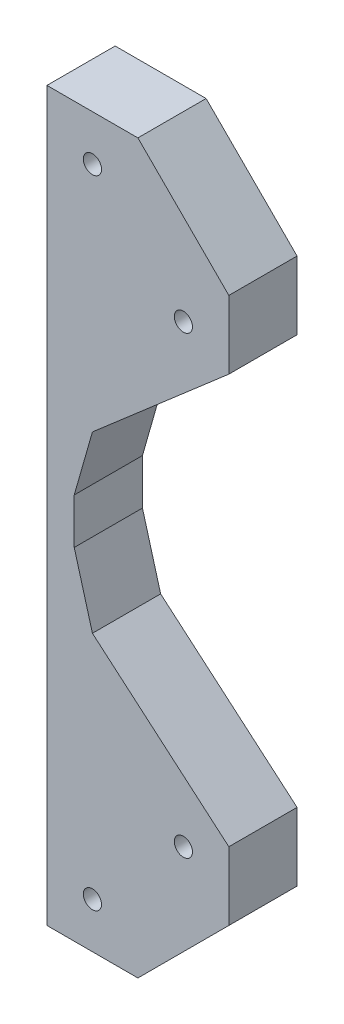
SolidWorks part; units mm, degrees
material "Náilon 101"
ref_plane "Plano frontal" through (0, 0, 0) normal (0, 0, 1) x (1, 0, 0)
ref_plane "Plano superior" through (0, 0, 0) normal (0, 1, 0) x (1, 0, 0)
ref_plane "Plano direito" through (0, 0, 0) normal (1, 0, 0) x (0, 0, -1)
sketch "Esboço1" plane through (0, 0, 0) normal (0, 0, 1) x (1, 0, 0)
  line L0 (0, 85.0753) -> (20, 85.0753)
  line L1 (20, 85.0753) -> (40, 65.0753)
  line L2 (40, 65.0753) -> (40, 50.0753)
  line L3 (40, 50.0753) -> (10, 24.0753)
  line L4 (6, 10.075) -> (10, 24.0753)
  line L5 (6, 10.075) -> (6, 0.075)
  line L6 (6, 0.075) -> (10, -14.2721)
  line L7 (10, -14.2721) -> (40, -39.9253)
  line L8 (40, -39.9253) -> (40, -54.9247)
  line L9 (20, -74.9247) -> (40, -54.9247)
  line L10 (20, -74.9247) -> (0, -74.9247)
  line L11 (0, -74.9247) -> (0, 85.0753)
  circle A0 centre (10, 75.0753) radius 2
  circle A1 centre (30, 55.0753) radius 2
  circle A2 centre (30, -44.9247) radius 2
  circle A3 centre (10, -64.9247) radius 2
extrude "Ressalto-extrusão1" add sketch "Esboço1" along normal blind 15
sketch "Esboço2" plane through (0, 0, 15) normal (0, 0, 1) x (1, 0, 0)
  line L12 (0, 85.0753) -> (0, -74.9247)
  line L13 (0, -74.9247) -> (20, -74.9247)
  line L14 (20, -74.9247) -> (40, -54.9247)
  line L15 (40, -54.9247) -> (40, -39.9253)
  line L16 (40, -39.9253) -> (10, -14.2721)
  line L17 (10, -14.2721) -> (6, 0.075)
  line L18 (6, 0.075) -> (6, 10.075)
  line L19 (6, 10.075) -> (10, 24.0753)
  line L20 (10, 24.0753) -> (40, 50.0753)
  line L21 (40, 50.0753) -> (40, 65.0753)
  line L22 (40, 65.0753) -> (20, 85.0753)
  line L23 (20, 85.0753) -> (0, 85.0753)
  line L24 (0, 85.0753) -> (0, -74.9247)
  line L25 (0, -74.9247) -> (20, -74.9247)
  line L26 (20, -74.9247) -> (40, -54.9247)
  line L27 (40, -54.9247) -> (40, -39.9253)
  line L28 (40, -39.9253) -> (10, -14.2721)
  line L29 (10, -14.2721) -> (6, 0.075)
  line L30 (6, 0.075) -> (6, 10.075)
  line L31 (6, 10.075) -> (10, 24.0753)
  line L32 (10, 24.0753) -> (40, 50.0753)
  line L33 (40, 50.0753) -> (40, 65.0753)
  line L34 (40, 65.0753) -> (20, 85.0753)
  line L35 (20, 85.0753) -> (0, 85.0753)
  circle A0 centre (30, -44.9247) radius 2 construction
  circle A1 centre (10, -64.9247) radius 2 construction
  circle A2 centre (30, 55.0753) radius 2 construction
  circle A3 centre (10, 75.0753) radius 2 construction
  circle A4 centre (30, -44.9247) radius 2
  circle A5 centre (10, -64.9247) radius 2
  circle A6 centre (30, 55.0753) radius 2
  circle A7 centre (10, 75.0753) radius 2
  dimension "D1" = 0
